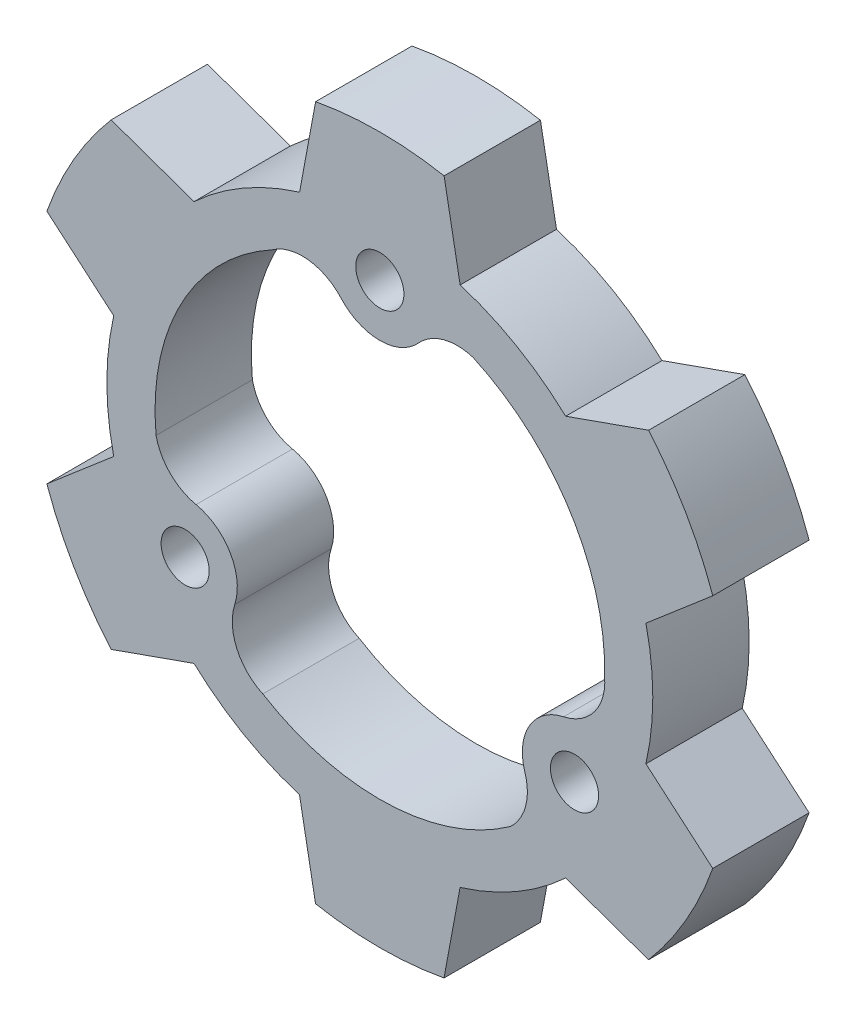
SolidWorks part; units mm, degrees
ref_plane "Plan de face" through (0, 0, 0) normal (0, 0, 1) x (1, 0, 0)
ref_plane "Plan de dessus" through (0, 0, 0) normal (0, 1, 0) x (1, 0, 0)
ref_plane "Plan de droite" through (0, 0, 0) normal (1, 0, 0) x (0, 0, -1)
sketch "Esquisse1" plane through (0, 0, 0) normal (0, 0, 1) x (1, 0, 0)
  line L0 (0, 14) -> (-12.125, -7.0011) construction
  line L1 (-12.125, -7.0011) -> (12.125, -7.0011) construction
  line L2 (12.125, -7.0011) -> (0, 14) construction
  line L6 (-4.9973, 16.2489) -> (-3.9973, 21.6338)
  line L8 (5.0027, 16.2472) -> (4.0027, 21.6328)
  line L9 (11.5733, 12.4522) -> (16.7368, 14.2786)
  line L10 (16.5719, 3.7911) -> (20.7359, 7.3499)
  line L11 (16.5706, -3.7967) -> (20.7341, -7.3552)
  line L12 (11.5692, -12.4561) -> (16.7332, -14.2829)
  line L13 (4.9973, -16.2489) -> (3.9973, -21.6338)
  line L14 (-5.0027, -16.2472) -> (-4.0027, -21.6328)
  line L15 (-11.5733, -12.4522) -> (-16.7368, -14.2786)
  line L16 (-16.5719, -3.7911) -> (-20.7359, -7.3499)
  line L17 (-16.5706, 3.7967) -> (-20.7341, 7.3552)
  line L18 (-11.5692, 12.4561) -> (-16.7332, 14.2829)
  circle A2 centre (0, 14) radius 1.5
  arc A12 (-2.411, 11.8207) -> (2.411, 11.8207) centre (0, 14) ccw
  arc A16 (5.8094, 12.7378) -> (2.411, 11.8207) centre (4.8221, 9.6414) ccw
  arc A17 (-2.411, 11.8207) -> (-6.7074, 12.2887) centre (-4.8221, 9.6414) ccw
  arc A18 (-6.7074, 12.2887) -> (-13.9359, -1.3378) centre (0, 0) ccw
  arc A19 (8.1265, -11.4) -> (9.0315, -7.9984) centre (5.9386, -8.9967) ccw
  arc A20 (11.4425, -3.8223) -> (9.0315, -7.9984) centre (12.1244, -7) ccw
  arc A21 (11.4425, -3.8223) -> (13.996, -0.3356) centre (10.7607, -0.6447) ccw
  circle A22 centre (12.1244, -7) radius 1.5
  arc A23 (-13.9359, -1.3378) -> (-11.4425, -3.8223) centre (-10.7607, -0.6447) ccw
  arc A24 (-9.0315, -7.9984) -> (-11.4425, -3.8223) centre (-12.1244, -7) ccw
  arc A25 (-9.0315, -7.9984) -> (-7.2886, -11.9531) centre (-5.9386, -8.9967) ccw
  circle A26 centre (-12.1244, -7) radius 1.5
  arc A27 (-7.2886, -11.9531) -> (8.1265, -11.4) centre (0, 0) ccw
  arc A28 (13.996, -0.3356) -> (5.8094, 12.7378) centre (0, 0) ccw
  circle A29 centre (0, 14) radius 3.25 construction
  arc A30 (4.0027, 21.6328) -> (-3.9973, 21.6338) centre (0, 0) ccw
  arc A31 (-4.9973, 16.2489) -> (-11.5692, 12.4561) centre (0, 0) ccw
  arc A32 (20.7359, 7.3499) -> (16.7368, 14.2786) centre (0, 0) ccw
  arc A33 (16.7332, -14.2829) -> (20.7341, -7.3552) centre (0, 0) ccw
  arc A34 (-4.0027, -21.6328) -> (3.9973, -21.6338) centre (0, 0) ccw
  arc A35 (-20.7359, -7.3499) -> (-16.7368, -14.2786) centre (0, 0) ccw
  arc A36 (-16.7332, 14.2829) -> (-20.7341, 7.3552) centre (0, 0) ccw
  arc A37 (11.5733, 12.4522) -> (5.0027, 16.2472) centre (0, 0) ccw
  arc A38 (16.5706, -3.7967) -> (16.5719, 3.7911) centre (0, 0) ccw
  arc A39 (4.9973, -16.2489) -> (11.5692, -12.4561) centre (0, 0) ccw
  arc A40 (-11.5733, -12.4522) -> (-5.0027, -16.2472) centre (0, 0) ccw
  arc A41 (-16.5706, 3.7967) -> (-16.5719, -3.7911) centre (0, 0) ccw
  point P31 (0, 0)
  point P56 (0, 0)
  dimension "D2" = 3
  dimension "D3" = 3
  dimension "D4" = 6.5
  dimension "D5" = 14
  dimension "D8" = 14
  dimension "D9" = 3.25
  dimension "D10" = 14
  dimension "D11" = 3.25
  dimension "D12" = 24.25
  dimension "D13" = 24.25
  dimension "D16" = 44
  dimension "D6" = 60
  dimension "D7" = 60
  dimension "D14" = 10.78
  dimension "D15" = 10.78
  dimension "D17" = 10
  dimension "D18" = 5.48
  dimension "D19" = 8
  dimension "D20" = 1
  dimension "D21" = 6
extrude "Boss.-Extru.2" add sketch "Esquisse1" along normal blind 6
